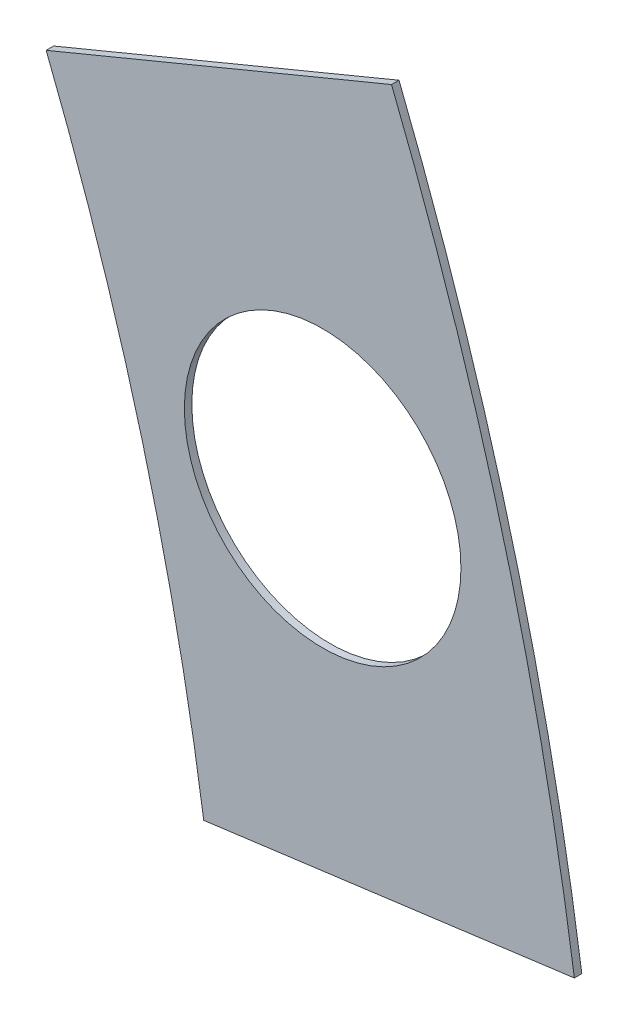
SolidWorks part; units mm, degrees
material "Copper"
ref_plane "Front Plane" through (0, 0, 0) normal (0, 0, 1) x (1, 0, 0)
ref_plane "Top Plane" through (0, 0, 0) normal (0, 1, 0) x (1, 0, 0)
ref_plane "Right Plane" through (0, 0, 0) normal (1, 0, 0) x (0, 0, -1)
sketch "Sketch1" plane through (0, 0, 0) normal (0, 0, 1) x (1, 0, 0)
  line L0 (0, 0) -> (320.3893, 0) construction
  line L1 (0, 0) -> (155.5285, 155.5285) construction
  line L2 (67.2115, 76.1917) -> (8.6967, 17.6769)
  line L3 (8.6967, 17.6769) -> (7.229, 14.1336)
  line L4 (101.4014, -6.35) -> (18.6489, -6.35)
  line L5 (15.1056, -4.8823) -> (18.6489, -6.35)
  line L6 (88.6729, 6.35) -> (27.8605, 6.35)
  line L9 (67.1914, 58.2111) -> (24.1905, 15.2102)
  line L10 (0, 0) -> (40.4486, 97.6516) construction
  line L11 (0, 0) -> (123.4567, -51.1374) construction
  line L18 (8.6967, 17.6769) -> (13.294, 8.6183) construction
  line L19 (18.6489, -6.35) -> (15.4943, 3.3063) construction
  line L20 (27.8605, 6.35) -> (27.7442, 6.7059) construction
  line L21 (24.1905, 15.2102) -> (24.3599, 14.8764) construction
  arc A0 (7.229, 14.1336) -> (15.1056, -4.8823) centre (0, 0) cw
  arc A1 (67.2115, 76.1917) -> (101.4014, -6.35) centre (0, 0) cw
  arc A2 (24.1905, 15.2102) -> (27.8605, 6.35) centre (0, 0) cw
  arc A3 (67.1914, 58.2111) -> (88.6729, 6.35) centre (0, 0) cw
  arc A8 (13.294, 8.6183) -> (15.4943, 3.3063) centre (0, 0) cw construction
  arc A9 (24.3599, 14.8764) -> (27.7442, 6.7059) centre (0, 0) cw construction
  dimension "D1" = 45
  dimension "D3" = 6.35
  dimension "D4" = 15.875
  dimension "D7" = 22.5
  dimension "D8" = 101.6
  dimension "D11" = 12.7
  dimension "D12" = 12.7
  dimension "D2" = 6.35
  dimension "D5" = 67.5
  dimension "D9" = 1.27
  dimension "D10" = 1.27
  dimension "D6" = 12.7
extrude "Boss-Extrude1" add sketch "Sketch1" along normal blind 0.254
sketch "Sketch2" plane through (0, 0, 0.254) normal (0, 0, 1) x (1, 0, 0)
  line L0 (0, 0) -> (101.6, 0) construction
  line L1 (0, 0) -> (71.842, 71.842) construction
  line L3 (0, 0) -> (22.225, 0) construction
  line L4 (0, 0) -> (15.7154, 15.7154) construction
  line L5 (0, 0) -> (95.25, 0) construction
  line L6 (0, 0) -> (92.0044, 24.6525) construction
  arc A0 (101.4014, -6.35) -> (67.2115, 76.1917) centre (0, 0) ccw construction
  circle A1 centre (22.225, 0) radius 4.699
  arc A2 (15.1056, -4.8823) -> (7.229, 14.1336) centre (0, 0) ccw construction
  circle A3 centre (36.195, 0) radius 4.699
  circle A4 centre (61.722, 0) radius 4.699
  circle A5 centre (75.692, 0) radius 4.699
  circle A6 centre (95.25, 0) radius 4.699
  circle A7 centre (15.7154, 15.7154) radius 4.699
  circle A8 centre (25.5937, 25.5937) radius 4.699
  circle A9 centre (43.644, 43.644) radius 4.699
  circle A10 centre (53.5223, 53.5223) radius 4.699
  circle A11 centre (92.0044, 24.6525) radius 4.699
  circle A12 centre (82.4889, 47.625) radius 4.699
  circle A13 centre (67.3519, 67.3519) radius 4.699
  dimension "D3" = 9.398
  dimension "D1" = 45
  dimension "D2" = 6.35
  dimension "D4" = 6.35
  dimension "D5" = 13.97
  dimension "D7" = 13.97
  dimension "D8" = 19.558
  dimension "D9" = 45
  dimension "D10" = 15
  dimension "D11" = 25.527
  dimension "D6" = 2
extrude "Cut-Extrude1" cut sketch "Sketch2" against normal through all
sketch "Sketch3" plane through (0, 0, 0.254) normal (0, 0, 1) x (1, 0, 0)
  line L0 (15.2664, 24.2467) -> (17.0625, 26.0427)
  line L1 (15.2664, 24.2467) -> (15.7154, 23.7977)
  line L2 (17.0625, 26.0427) -> (17.5115, 25.5937)
  line L3 (15.7154, 23.7977) -> (17.5115, 25.5937)
  line L4 (67.2115, 76.1917) -> (8.6967, 17.6769) construction
  line L5 (44.9911, 53.9713) -> (43.195, 52.1753)
  line L6 (44.9911, 53.9713) -> (45.4401, 53.5223)
  line L7 (43.195, 52.1753) -> (43.644, 51.7263)
  line L8 (45.4401, 53.5223) -> (43.644, 51.7263)
  line L9 (27.94, -6.35) -> (30.48, -6.35)
  line L10 (27.94, -6.35) -> (27.94, -5.715)
  line L11 (30.48, -6.35) -> (30.48, -5.715)
  line L12 (27.94, -5.715) -> (30.48, -5.715)
  line L13 (18.6489, -6.35) -> (101.4014, -6.35) construction
  line L14 (67.437, -6.35) -> (69.977, -6.35)
  line L15 (67.437, -6.35) -> (67.437, -5.715)
  line L16 (69.977, -6.35) -> (69.977, -5.715)
  line L17 (67.437, -5.715) -> (69.977, -5.715)
  line L18 (29.2307, 38.211) -> (31.0268, 40.007)
  line L19 (29.2307, 38.211) -> (29.6797, 37.762)
  line L20 (31.0268, 40.007) -> (31.4758, 39.558)
  line L21 (29.6797, 37.762) -> (31.4758, 39.558)
  line L22 (56.845, 65.8253) -> (55.049, 64.0292)
  line L23 (56.845, 65.8253) -> (57.294, 65.3763)
  line L24 (55.049, 64.0292) -> (55.498, 63.5802)
  line L25 (57.294, 65.3763) -> (55.498, 63.5802)
  line L26 (47.6885, -6.35) -> (50.2285, -6.35)
  line L27 (47.6885, -6.35) -> (47.6885, -5.715)
  line L28 (50.2285, -6.35) -> (50.2285, -5.715)
  line L29 (47.6885, -5.715) -> (50.2285, -5.715)
  line L30 (84.201, -6.35) -> (86.741, -6.35)
  line L31 (84.201, -6.35) -> (84.201, -5.715)
  line L32 (86.741, -6.35) -> (86.741, -5.715)
  line L33 (84.201, -5.715) -> (86.741, -5.715)
  line L34 (0, 0) -> (100.7308, 13.2615) construction
  line L35 (0, 0) -> (93.8662, 38.8806) construction
  line L36 (0, 0) -> (80.6047, 61.8502) construction
  line L37 (0, 0) -> (101.6, 0) construction
  line L38 (99.9355, 14.4377) -> (100.267, 11.9194)
  line L39 (99.9355, 14.4377) -> (101.1946, 14.6035)
  line L40 (100.267, 11.9194) -> (101.5261, 12.0852)
  line L41 (101.1946, 14.6035) -> (101.5261, 12.0852)
  line L42 (99.9355, 14.4377) -> (101.5261, 12.0852) construction
  line L43 (100.267, 11.9194) -> (101.1946, 14.6035) construction
  line L44 (93.7655, 37.4643) -> (94.9388, 37.9503)
  line L45 (93.7655, 37.4643) -> (92.7935, 39.811)
  line L46 (94.9388, 37.9503) -> (93.9668, 40.297)
  line L47 (92.7935, 39.811) -> (93.9668, 40.297)
  line L48 (93.7655, 37.4643) -> (93.9668, 40.297) construction
  line L49 (94.9388, 37.9503) -> (92.7935, 39.811) construction
  line L50 (79.3278, 62.4712) -> (80.874, 60.456)
  line L51 (79.3278, 62.4712) -> (80.3354, 63.2443)
  line L52 (80.874, 60.456) -> (81.8816, 61.2292)
  line L53 (80.3354, 63.2443) -> (81.8816, 61.2292)
  line L54 (79.3278, 62.4712) -> (81.8816, 61.2292) construction
  line L55 (80.874, 60.456) -> (80.3354, 63.2443) construction
  line L56 (13.5939, 7.0054) -> (14.5659, 4.6588)
  line L57 (13.5939, 7.0054) -> (14.7672, 7.4914)
  line L58 (14.5659, 4.6588) -> (15.7393, 5.1448)
  line L59 (14.7672, 7.4914) -> (15.7393, 5.1448)
  line L60 (13.5939, 7.0054) -> (15.7393, 5.1448) construction
  line L61 (14.5659, 4.6588) -> (14.7672, 7.4914) construction
  circle A0 centre (15.7154, 15.7154) radius 4.699 construction
  circle A1 centre (43.644, 43.644) radius 4.699 construction
  circle A2 centre (22.225, 0) radius 4.699 construction
  circle A3 centre (61.722, 0) radius 4.699 construction
  arc A4 (101.4014, -6.35) -> (67.2115, 76.1917) centre (0, 0) ccw construction
  arc A9 (15.1056, -4.8823) -> (7.229, 14.1336) centre (0, 0) ccw construction
  circle A10 centre (36.195, 0) radius 4.699 construction
  circle A11 centre (75.692, 0) radius 4.699 construction
  circle A12 centre (25.5937, 25.5937) radius 4.699 construction
  circle A13 centre (53.5223, 53.5223) radius 4.699 construction
  point P75 (14.6666, 6.0751)
  dimension "D2" = 5.715
  dimension "D3" = 2.54
  dimension "D6" = 5.715
  dimension "D8" = 0.635
  dimension "D9" = 5.715
  dimension "D12" = 5.715
  dimension "D4" = 7.5
  dimension "D5" = 22.5
  dimension "D7" = 37.5
  dimension "D10" = 90
  dimension "D11" = 1.27
  dimension "D14" = 0.635
  dimension "D15" = 90
  dimension "D18" = 0.635
  dimension "D19" = 90
  dimension "D22" = 0.635
  dimension "D20" = 1.27
  dimension "D17" = 0.635
  dimension "D13" = 11.4935
  dimension "D16" = 8.509
  dimension "D21" = 11.4935
  dimension "D23" = 8.509
extrude "Cut-Extrude2" cut sketch "Sketch3" against normal through all
sketch "Sketch5" plane through (0, 0, 0.254) normal (0, 0, 1) x (1, 0, 0)
  line L0 (0, 0) -> (99.623, 41.2652) construction
  line L1 (0, 0) -> (107.1415, 14.1054) construction
  line L2 (86.741, -6.35) -> (101.4014, -6.35) construction
  line L3 (100.267, 11.9194) -> (100.8887, 12.0013) construction
  line L4 (69.977, -6.35) -> (84.201, -6.35) construction
  line L5 (81.4371, 32.3577) -> (95.5183, 38.1903)
  line L6 (93.3728, 40.0509) -> (92.7935, 39.811) construction
  line L8 (86.7054, 12.6959) -> (101.8164, 14.6853)
  arc A0 (86.7054, 12.6959) -> (81.4371, 32.3577) centre (0, 0) ccw
  arc A1 (95.5183, 38.1903) -> (101.8164, 14.6853) centre (0, 0) cw
  arc A2 (88.6729, 6.35) -> (67.1914, 58.2111) centre (0, 0) ccw construction
  arc A3 (100.5572, 14.5196) -> (94.3448, 37.7043) centre (0, 0) ccw construction
  dimension "D3" = 1.27
  dimension "D4" = 1.27
  dimension "D1" = 7.5
  dimension "D2" = 22.5
  dimension "D5" = 2.54
  dimension "D6" = 2.54
extrude "Cut-Extrude5" cut sketch "Sketch5" against normal through all flip side to cut
equation "\"cSep\"= 1.005"
equation "\"D11@Sketch2\"=\"cSep\""
equation "\"cSep2\"= \"D8@Sketch2\""
equation "\"D13@Sketch3\"=\"cSep\"/2-.05"
equation "\"D16@Sketch3\"=\"cSep2\"/2-.05"
equation "\"D21@Sketch3\"=\"cSep\"/2-.05"
equation "\"D23@Sketch3\"=\"cSep2\"/2-.05"
